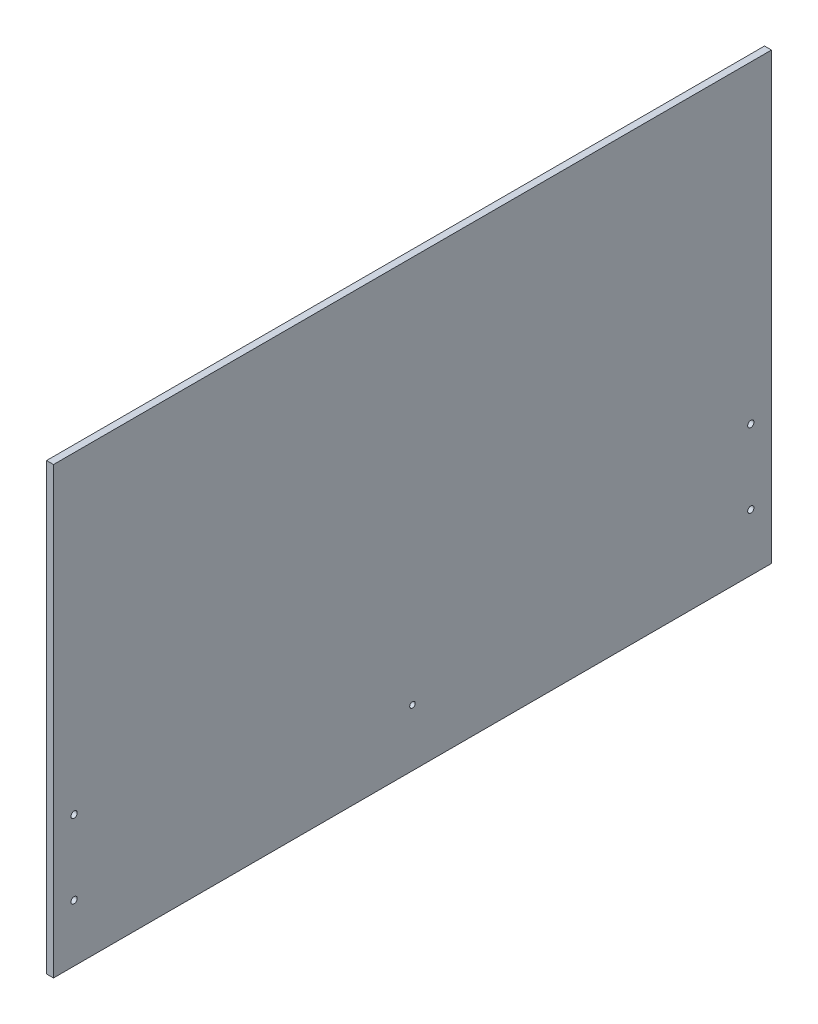
SolidWorks part; units mm, degrees
ref_plane "Front Plane" through (0, 0, 0) normal (0, 0, 1) x (1, 0, 0)
ref_plane "Top Plane" through (0, 0, 0) normal (0, 1, 0) x (1, 0, 0)
ref_plane "Right Plane" through (0, 0, 0) normal (1, 0, 0) x (0, 0, -1)
sketch "Sketch1" plane through (0, 0, 0) normal (1, 0, 0) x (0, 0, -1)
  line L1 (-246.0625, -152.4) -> (246.0625, -152.4)
  line L2 (-246.0625, -152.4) -> (-246.0625, 152.4)
  line L3 (-246.0625, 152.4) -> (246.0625, 152.4)
  line L4 (246.0625, -152.4) -> (246.0625, 152.4)
  line L5 (-246.0625, -152.4) -> (246.0625, 152.4) construction
  line L6 (-246.0625, 152.4) -> (246.0625, -152.4) construction
  point P0 (0, 0)
  dimension "D1" = 304.8
  dimension "D2" = 492.125
extrude "Boss-Extrude1" add sketch "Sketch1" along normal blind 4.7625
sketch "Sketch2" plane through (4.7625, 0, 0) normal (1, 0, 0) x (0, 0, -1)
  line L0 (0, 0) -> (42.4264, 42.4264) construction
  line L1 (-24.8528, -60) -> (24.8528, -60)
  line L2 (-60, -24.8528) -> (-60, 24.8528)
  line L3 (-24.8528, 60) -> (24.8528, 60)
  line L4 (60, -24.8528) -> (60, 24.8528)
  line L5 (-42.4264, -42.4264) -> (42.4264, 42.4264) construction
  line L6 (0, 0) -> (-42.4264, 42.4264) construction
  line L7 (-42.4264, 42.4264) -> (-24.8528, 60) construction
  line L8 (0, 0) -> (42.4264, -42.4264) construction
  line L9 (-42.4264, 42.4264) -> (-60, 24.8528) construction
  line L10 (42.4264, -42.4264) -> (24.8528, -60) construction
  line L11 (42.4264, -42.4264) -> (60, -24.8528) construction
  line L12 (0, 0) -> (0, 60) construction
  line L13 (0, 0) -> (0, -60) construction
  line L14 (42.4264, 42.4264) -> (60, 24.8528) construction
  line L15 (42.4264, 42.4264) -> (24.8528, 60) construction
  line L16 (-42.4264, -42.4264) -> (-24.8528, -60) construction
  line L17 (-42.4264, -42.4264) -> (-60, -24.8528) construction
  line L18 (-24.8528, 60) -> (-60, 24.8528)
  line L19 (24.8528, 60) -> (60, 24.8528)
  line L20 (42.4264, -42.4264) -> (60, -24.8528)
  line L21 (24.8528, -60) -> (42.4264, -42.4264)
  line L22 (-60, -24.8528) -> (-24.8528, -60)
  point P0 (0, 0)
  dimension "D2" = 60
extrude "Cut-Extrude1" cut sketch "Sketch2" against normal up to next
sketch "Sketch3" plane through (0, 0, 246.0625) normal (0, 0, 1) x (1, 0, 0)
  line L1 (0, 152.4) -> (4.7625, 152.4)
  line L2 (0, 152.4) -> (0, -152.4)
  line L3 (0, -152.4) -> (4.7625, -152.4)
  line L4 (4.7625, 152.4) -> (4.7625, -152.4)
extrude "Boss-Extrude2" add sketch "Sketch3" against normal up to next
hole_wizard "#8 Clearance Hole1" positions "Sketch5" profile "Sketch4" hole size "#8" standard "ANSI Inch"
sketch "Sketch5" plane through (4.7625, 0, 0) normal (1, 0, 0) x (0, 0, -1)
  line L1 (-246.0625, 152.4) -> (-246.0625, -152.4) construction
  line L2 (-246.0625, -152.4) -> (246.0625, -152.4) construction
  line L3 (246.0625, -152.4) -> (246.0625, 152.4) construction
  point P0 (-231.9337, -113.284)
  point P2 (-231.9337, -62.484)
  point P4 (231.9338, -62.484)
  point P6 (231.9338, -113.284)
  dimension "D1" = 14.1287
  dimension "D2" = 89.916
  dimension "D3" = 39.116
  dimension "D4" = 14.1288
sketch "Sketch4" plane through (4.7625, -113.284, 231.9337) normal (0, 1, 0) x (0, 0, -1)
  line L0 (0, 0) -> (0, 75.7154)
  line L1 (0, 75.7154) -> (2.1526, 74.422)
  line L2 (2.1526, 74.422) -> (2.1526, 0)
  line L5 (2.1526, 0) -> (0, 0)
  line L10 (0, 75.7154) -> (-2.1527, 74.422) construction
  line L11 (0, -6.35) -> (0, 107.95) construction
  dimension "Hole Dia." = 4.3053
  dimension "Hole Depth" = 74.422
  dimension "Drill Angle" = 118
hole_wizard "#6 Clearance Hole1" positions "Sketch7" profile "Sketch6" hole size "#6" standard "ANSI Inch"
sketch "Sketch7" plane through (4.7625, 0, 0) normal (1, 0, 0) x (0, 0, -1)
  line L0 (-231.9337, -113.284) -> (231.9338, -113.284) construction
  point P0 (0, -113.284)
  point P11 (0, -113.284)
sketch "Sketch6" plane through (4.7625, -113.284, 0) normal (0, 1, 0) x (0, 0, -1)
  line L0 (0, 0) -> (0, 26.5408)
  line L1 (0, 26.5408) -> (1.8986, 25.4)
  line L2 (1.8986, 25.4) -> (1.8986, 0)
  line L5 (1.8986, 0) -> (0, 0)
  line L10 (0, 26.5408) -> (-1.8987, 25.4) construction
  line L11 (0, -6.35) -> (0, 107.95) construction
  dimension "Hole Dia." = 3.7973
  dimension "Hole Depth" = 25.4
  dimension "Drill Angle" = 118
